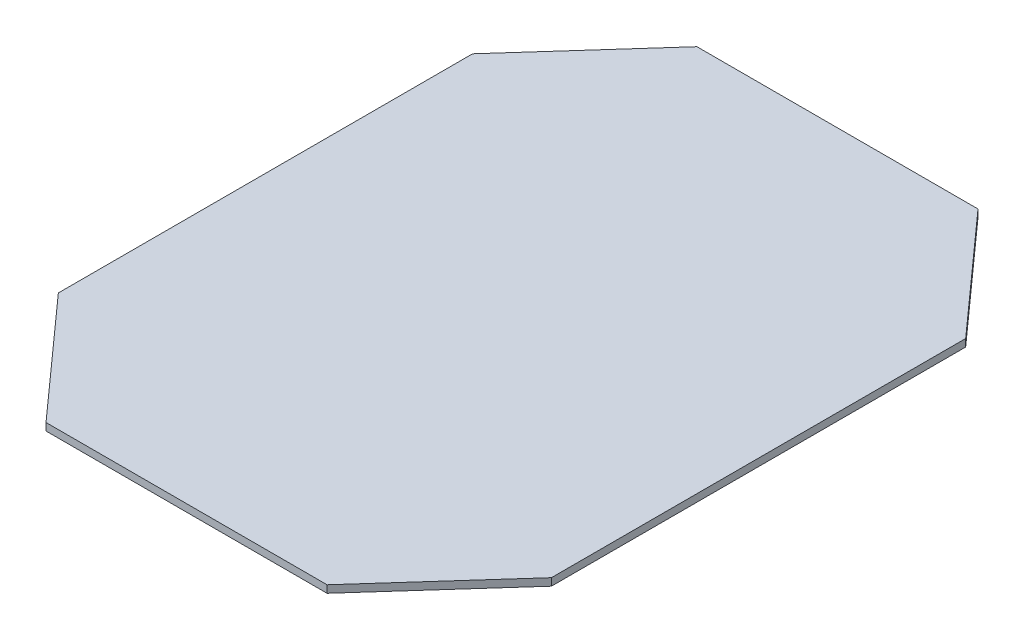
SolidWorks part; units mm, degrees
ref_plane "Front Plane" through (0, 0, 0) normal (0, 0, 1) x (1, 0, 0)
ref_plane "Top Plane" through (0, 0, 0) normal (0, 1, 0) x (1, 0, 0)
ref_plane "Right Plane" through (0, 0, 0) normal (1, 0, 0) x (0, 0, -1)
sketch "Sketch1" plane through (0, 0, 0) normal (0, 1, 0) x (1, 0, 0)
  line L1 (0, 0) -> (100, 0)
  line L2 (0, 0) -> (0, 132)
  line L3 (0, 132) -> (100, 132)
  line L4 (100, 0) -> (100, 132)
  dimension "D1" = 100
  dimension "D2" = 132
extrude "Boss-Extrude1" add sketch "Sketch1" along normal blind 1.5
sketch "Sketch2" plane through (0, 1.5, 0) normal (0, 1, 0) x (1, 0, 0)
  line L0 (50, 132) -> (100, 66) construction
  line L1 (100, 132) -> (0, 132) construction
  line L2 (100, 0) -> (100, 132) construction
  line L3 (50, 132) -> (50, 139.5538) construction
  line L4 (100, 66) -> (143.771, 66) construction
  line L5 (50, 132) -> (78.5, 132) construction
  line L6 (100, 66) -> (100, 108) construction
  line L7 (78.5, 132) -> (100, 108)
  line L8 (100, 108) -> (126.7907, 132)
  line L9 (126.7907, 132) -> (105.2907, 156)
  line L10 (105.2907, 156) -> (78.5, 132)
  line L11 (-26.7907, 132) -> (-5.2907, 156)
  line L12 (0, 108) -> (-26.7907, 132)
  line L13 (21.5, 132) -> (0, 108)
  line L14 (-5.2907, 156) -> (21.5, 132)
  line L15 (126.7907, 0) -> (105.2907, -24)
  line L16 (100, 24) -> (126.7907, 0)
  line L17 (78.5, 0) -> (100, 24)
  line L18 (105.2907, -24) -> (78.5, 0)
  line L19 (0, 24) -> (-26.7907, 0)
  line L20 (21.5, 0) -> (0, 24)
  line L21 (-5.2907, -24) -> (21.5, 0)
  line L22 (-26.7907, 0) -> (-5.2907, -24)
  dimension "D1" = 28.5
  dimension "D2" = 42
extrude "Cut-Extrude1" cut sketch "Sketch2" against normal blind 1.5
